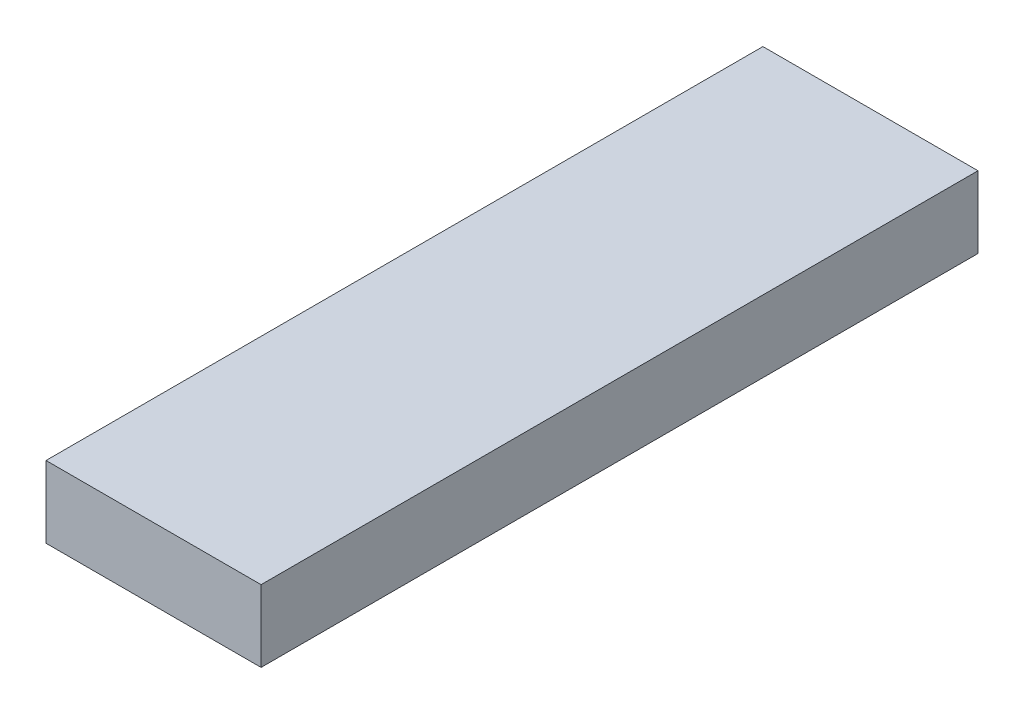
SolidWorks part; units mm, degrees
ref_plane "Front Plane" through (0, 0, 0) normal (0, 0, 1) x (1, 0, 0)
ref_plane "Top Plane" through (0, 0, 0) normal (0, 1, 0) x (1, 0, 0)
ref_plane "Right Plane" through (0, 0, 0) normal (1, 0, 0) x (0, 0, -1)
sketch "Sketch1" plane through (0, 0, 0) normal (0, 0, 1) x (1, 0, 0)
  line L1 (0, 0) -> (9, 0)
  line L2 (0, 0) -> (0, 3)
  line L3 (0, 3) -> (9, 3)
  line L4 (9, 0) -> (9, 3)
  dimension "D1" = 9
  dimension "D2" = 3
extrude "Boss-Extrude1" add sketch "Sketch1" along normal blind 30
